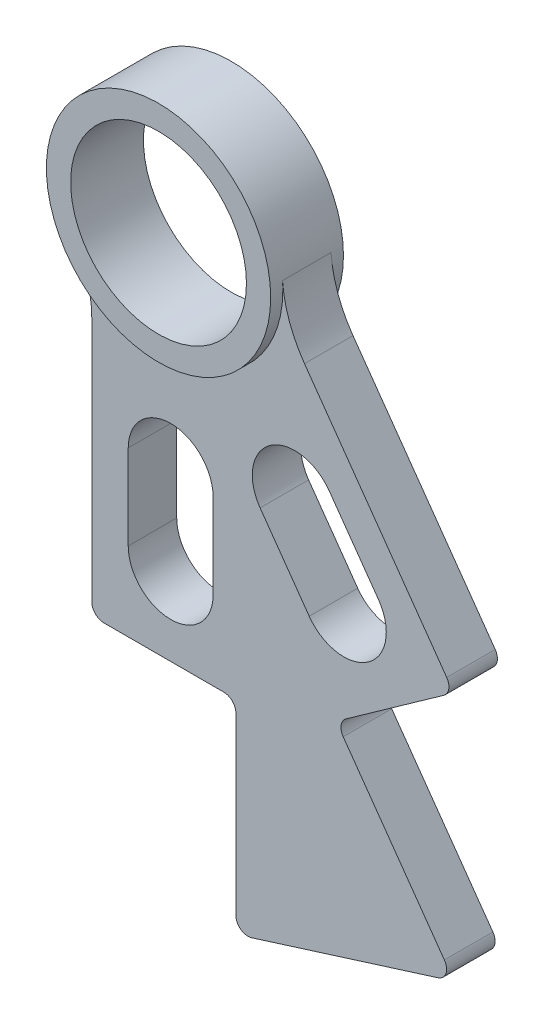
SolidWorks part; units mm, degrees
material "AISI 4130 Steel, annealed at 865C"
ref_plane "X-Y Datum" through (0, 0, 0) normal (0, 0, 1) x (1, 0, 0)
ref_plane "X-Z Datum" through (0, 0, 0) normal (0, 1, 0) x (1, 0, 0)
ref_plane "Y-Z Datum" through (0, 0, 0) normal (1, 0, 0) x (0, 0, -1)
sketch "Sketch1" plane through (0, 0, 0) normal (0, 0, 1) x (1, 0, 0)
  line L0 (0, -39.0706) -> (0, -27.9581) construction
  line L1 (-5.5562, -39.0706) -> (-5.5562, -27.9581)
  line L2 (5.5562, -39.0706) -> (5.5562, -27.9581)
  line L3 (22.6674, -31.9787) -> (16.2412, -22.9128) construction
  line L4 (18.1344, -35.1918) -> (11.7082, -26.1259)
  line L5 (27.2003, -28.7657) -> (20.7742, -19.6997)
  line L6 (-10.3187, -15.7343) -> (-10.3187, -49.3893)
  line L7 (-10.3187, -49.3893) -> (10.3187, -49.3893)
  line L10 (20.2161, -46.3643) -> (37.0529, -34.43)
  line L11 (37.0529, -34.43) -> (17.5173, -6.8694)
  line L12 (0, -39.0706) -> (0, 0) construction
  line L13 (0, 0) -> (22.6674, -31.9787) construction
  line L14 (0, -44.6268) -> (0, -49.3893) construction
  line L15 (25.8805, -36.5117) -> (28.6345, -40.3971) construction
  line L16 (23.9872, -24.2327) -> (27.8727, -21.4786) construction
  line L17 (-5.5562, -33.5143) -> (-10.3187, -33.5143) construction
  line L18 (-10.3187, -17.6393) -> (10.3187, -17.6393) construction
  line L19 (10.3187, -17.6393) -> (10.3187, -49.3893) construction
  line L20 (5.5562, -33.5143) -> (10.3187, -33.5143) construction
  line L21 (0, -22.4018) -> (0, -17.6393) construction
  line L22 (20.2161, -46.3643) -> (1.8556, -20.4616) construction
  line L23 (1.8556, -20.4616) -> (18.6924, -8.5272) construction
  line L24 (14.9213, -30.6589) -> (11.0359, -33.4129) construction
  line L25 (13.0281, -18.3798) -> (10.274, -14.4944) construction
  line L29 (8.5407, -49.3893) -> (8.5407, -79.8693)
  line L31 (8.5407, -79.8693) -> (39.2928, -70.2028)
  line L33 (39.2928, -70.2028) -> (21.6667, -45.3361)
  circle A0 centre (0, 0) radius 11.5062
  arc A1 (-5.5562, -39.0706) -> (5.5562, -39.0706) centre (0, -39.0706) ccw
  arc A2 (5.5562, -27.9581) -> (-5.5562, -27.9581) centre (0, -27.9581) ccw
  arc A3 (18.1344, -35.1918) -> (27.2003, -28.7657) centre (22.6674, -31.9787) ccw
  arc A4 (20.7742, -19.6997) -> (11.7082, -26.1259) centre (16.2412, -22.9128) ccw
  arc A5 (14.6392, 1.1103) -> (-12.5852, -7.5598) centre (0, 0) ccw
  arc A6 (17.5173, -6.8694) -> (14.6392, 1.1103) centre (30.4687, 2.3108) cw
  arc A7 (-10.3187, -15.7343) -> (-12.5852, -7.5598) centre (-26.1937, -15.7343) ccw
  arc A14 (-12.5852, -7.5598) -> (14.6392, 1.1103) centre (0, 0) ccw
  point P2 (8.5407, -49.3893)
  point P5 (0, -33.5143)
  point P11 (19.4543, -27.4458)
  point P17 (21.6667, -45.3361)
  point P24 (28.6345, -40.3971)
  point P31 (0, -49.3893)
  point P39 (25.8805, -36.5117)
  dimension "D1" = 23.0124
  dimension "D2" = 14.6812
  dimension "D8" = 15.875
  dimension "D9" = 35.33
  dimension "D3" = 1.778
  dimension "D4" = 4.7625
  dimension "D5" = 31.75
  dimension "D6" = 2.032
  dimension "D7" = 1.905
  dimension "D10" = 1.778
  dimension "D11" = 30.48
extrude "Boss-Extrude1" add sketch "Sketch1" along normal mid plane 9.525 contours A5 A14 A0
sketch "Sketch5" plane through (0, 0, 0) normal (0, 0, 1) x (1, 0, 0)
  line L0 (0, -39.0706) -> (0, -27.9581) construction
  line L1 (-5.5562, -39.0706) -> (-5.5562, -27.9581)
  line L2 (5.5562, -39.0706) -> (5.5562, -27.9581)
  line L3 (22.6674, -31.9787) -> (16.2412, -22.9128) construction
  line L4 (18.1344, -35.1918) -> (11.7082, -26.1259)
  line L5 (27.2003, -28.7657) -> (20.7742, -19.6997)
  line L6 (-10.3187, -15.7343) -> (-10.3187, -49.3893)
  line L7 (-10.3187, -49.3893) -> (10.3187, -49.3893)
  line L8 (20.2161, -46.3643) -> (37.0529, -34.43)
  line L9 (37.0529, -34.43) -> (17.5173, -6.8694)
  line L10 (0, -39.0706) -> (0, 0) construction
  line L11 (0, 0) -> (22.6674, -31.9787) construction
  line L12 (0, -44.6268) -> (0, -49.3893) construction
  line L13 (25.8805, -36.5117) -> (28.6345, -40.3971) construction
  line L14 (23.9872, -24.2327) -> (27.8727, -21.4786) construction
  line L15 (-5.5562, -33.5143) -> (-10.3187, -33.5143) construction
  line L16 (-10.3187, -17.6393) -> (10.3187, -17.6393) construction
  line L17 (10.3187, -17.6393) -> (10.3187, -49.3893) construction
  line L18 (5.5562, -33.5143) -> (10.3187, -33.5143) construction
  line L19 (0, -22.4018) -> (0, -17.6393) construction
  line L20 (20.2161, -46.3643) -> (1.8556, -20.4616) construction
  line L21 (1.8556, -20.4616) -> (18.6924, -8.5272) construction
  line L22 (14.9213, -30.6589) -> (11.0359, -33.4129) construction
  line L23 (13.0281, -18.3798) -> (10.274, -14.4944) construction
  line L24 (8.5407, -49.3893) -> (8.5407, -76.0593)
  line L25 (8.5407, -76.0593) -> (37.0896, -67.0944)
  line L26 (37.0896, -67.0944) -> (21.6667, -45.3361)
  circle A0 centre (0, 0) radius 11.5062
  arc A1 (-5.5562, -39.0706) -> (5.5562, -39.0706) centre (0, -39.0706) ccw
  arc A2 (5.5562, -27.9581) -> (-5.5562, -27.9581) centre (0, -27.9581) ccw
  arc A3 (18.1344, -35.1918) -> (27.2003, -28.7657) centre (22.6674, -31.9787) ccw
  arc A4 (20.7742, -19.6997) -> (11.7082, -26.1259) centre (16.2412, -22.9128) ccw
  arc A5 (14.6392, 1.1103) -> (-12.5852, -7.5598) centre (0, 0) ccw
  arc A6 (17.5173, -6.8694) -> (14.6392, 1.1103) centre (30.4687, 2.3108) cw
  arc A7 (-10.3187, -15.7343) -> (-12.5852, -7.5598) centre (-26.1937, -15.7343) ccw
  arc A8 (-12.5852, -7.5598) -> (14.6392, 1.1103) centre (0, 0) ccw
  point P2 (8.5407, -49.3893)
  point P5 (0, -33.5143)
  point P11 (19.4543, -27.4458)
  point P17 (21.6667, -45.3361)
  point P24 (28.6345, -40.3971)
  point P31 (0, -49.3893)
  point P39 (25.8805, -36.5117)
  dimension "D1" = 23.0124
  dimension "D3" = 15.875
  dimension "D7" = 14.6812
  dimension "D2" = 4.7625
  dimension "D4" = 31.75
  dimension "D5" = 1.905
  dimension "D6" = 2.032
  dimension "D8" = 35.33
  dimension "D9" = 1.778
  dimension "D10" = 1.778
  dimension "D11" = 26.67
extrude "Boss-Extrude2" add sketch "Sketch5" along normal mid plane 6.35
fillet "Fillet2" radius 1.5875 6 edges at (21.6667, -45.3361, 0) (37.0896, -67.0944, 0) (37.0529, -34.43, 0) (8.5407, -76.0593, 0) (8.5407, -49.3893, 0) (-10.3187, -49.3893, 0)
sketch "Sketch2" plane through (0, 0, 0) normal (0, 0, 1) x (1, 0, 0)
  line L0 (0, -39.0706) -> (0, -27.9581) construction
  line L1 (-5.5562, -39.0706) -> (-5.5562, -27.9581)
  line L2 (5.5562, -39.0706) -> (5.5562, -27.9581)
  line L3 (22.6674, -31.9787) -> (16.2412, -22.9128) construction
  line L4 (18.1344, -35.1918) -> (11.7082, -26.1259)
  line L5 (27.2003, -28.7657) -> (20.7742, -19.6997)
  line L6 (-10.3187, -15.7343) -> (-10.3187, -49.3893)
  line L7 (-10.3187, -49.3893) -> (10.3187, -49.3893)
  line L10 (20.2161, -46.3643) -> (37.0529, -34.43)
  line L11 (37.0529, -34.43) -> (17.5173, -6.8694)
  line L12 (0, -39.0706) -> (0, 0) construction
  line L13 (0, 0) -> (22.6674, -31.9787) construction
  line L14 (0, -44.6268) -> (0, -49.3893) construction
  line L15 (25.8805, -36.5117) -> (28.6345, -40.3971) construction
  line L16 (23.9872, -24.2327) -> (27.8727, -21.4786) construction
  line L17 (-5.5562, -33.5143) -> (-10.3187, -33.5143) construction
  line L18 (-10.3187, -17.6393) -> (10.3187, -17.6393) construction
  line L19 (10.3187, -17.6393) -> (10.3187, -49.3893) construction
  line L20 (5.5562, -33.5143) -> (10.3187, -33.5143) construction
  line L21 (0, -22.4018) -> (0, -17.6393) construction
  line L22 (20.2161, -46.3643) -> (1.8556, -20.4616) construction
  line L23 (1.8556, -20.4616) -> (18.6924, -8.5272) construction
  line L24 (14.9213, -30.6589) -> (11.0359, -33.4129) construction
  line L25 (13.0281, -18.3798) -> (10.274, -14.4944) construction
  line L30 (20.2161, -46.3643) -> (10.3187, -32.4012)
  line L32 (10.3187, -32.4012) -> (10.3187, -49.3893)
  arc A1 (-5.5562, -39.0706) -> (5.5562, -39.0706) centre (0, -39.0706) ccw
  arc A2 (5.5562, -27.9581) -> (-5.5562, -27.9581) centre (0, -27.9581) ccw
  arc A3 (18.1344, -35.1918) -> (27.2003, -28.7657) centre (22.6674, -31.9787) ccw
  arc A4 (20.7742, -19.6997) -> (11.7082, -26.1259) centre (16.2412, -22.9128) ccw
  arc A6 (17.5173, -6.8694) -> (14.6392, 1.1103) centre (30.4687, 2.3108) cw
  arc A7 (-10.3187, -15.7343) -> (-12.5852, -7.5598) centre (-26.1937, -15.7343) ccw
  arc A14 (-12.5852, -7.5598) -> (14.6392, 1.1103) centre (0, 0) ccw
  point P5 (0, -33.5143)
  point P11 (19.4543, -27.4458)
  point P24 (28.6345, -40.3971)
  point P31 (0, -49.3893)
  point P39 (25.8805, -36.5117)
  dimension "D1" = 7.5598
  dimension "D2" = 14.6812
  dimension "D8" = 15.875
  dimension "D9" = 35.33
  dimension "D3" = 20.6375
  dimension "D4" = 4.7625
  dimension "D5" = 31.75
  dimension "D6" = 2.032
  dimension "D7" = 1.905
sketch "Sketch3" plane through (0, 0, 4.7625) normal (0, 0, 1) x (1, 0, 0)
  point P0 (0, 0)
sketch "Sketch4" plane through (0, 0, 0) normal (0, 0, -1) x (-1, 0, 0)
  point P0 (0, 0)
  point P1 (0, 0)
  point P3 (0, 0)
